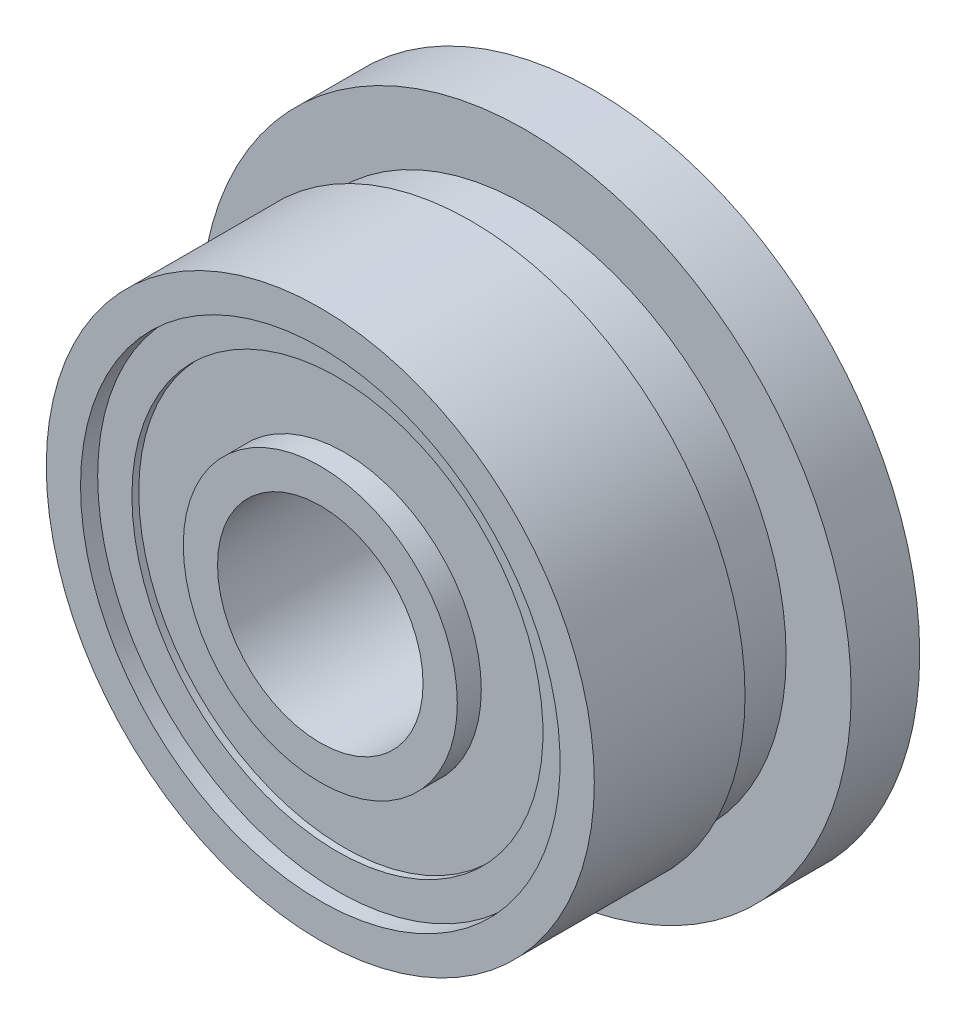
SolidWorks part; units mm, degrees
ref_plane "Piano frontale" through (0, 0, 0) normal (0, 0, 1) x (1, 0, 0)
ref_plane "Piano superiore" through (0, 0, 0) normal (0, 1, 0) x (1, 0, 0)
ref_plane "Piano destro" through (0, 0, 0) normal (1, 0, 0) x (0, 0, -1)
sketch "Schizzo1" plane through (0, 0, 0) normal (0, 0, 1) x (1, 0, 0)
  circle A0 centre (0, 0) radius 4
  dimension "D1" = 8
extrude "Estrusione-Estrusione1" add sketch "Schizzo1" along normal blind 4
sketch "Schizzo2" plane through (0, 0, 4) normal (0, 0, 1) x (1, 0, 0)
  circle A0 centre (0, 0) radius 1.5
  dimension "D1" = 3
extrude "Taglio-Estrusione1" cut sketch "Schizzo2" against normal through all
sketch "Schizzo3" plane through (0, 0, 0) normal (0, 0, -1) x (-1, 0, 0)
  circle A0 centre (0, 0) radius 3.5
  circle A1 centre (0, 0) radius 2
  dimension "D1" = 7
  dimension "D2" = 4
extrude "Taglio-Estrusione2" cut sketch "Schizzo3" against normal blind 0.25
sketch "Schizzo4" plane through (0, 0, 0.25) normal (0, 0, -1) x (-1, 0, 0)
  circle A0 centre (0, 0) radius 3
  circle A1 centre (0, 0) radius 2 construction
  circle A2 centre (0, 0) radius 2
  dimension "D1" = 6
extrude "Taglio-Estrusione3" cut sketch "Schizzo4" against normal blind 0.1
ref_plane "Piano1" through (0, 0, 2) normal (0, 0, 1) x (1, 0, 0)
mirror "Specchia1" about plane through (0, 0, 2) normal (0, 0, 1) of "Taglio-Estrusione3", "Taglio-Estrusione2"
sketch "Schizzo5" plane through (0, 0, 0) normal (0, 0, 1) x (1, 0, 0)
  circle A0 centre (0, 0) radius 4.75
  circle A1 centre (0, 0) radius 4 construction
  circle A2 centre (0, 0) radius 4
  dimension "D1" = 9.5
extrude "Estrusione-Estrusione2" add sketch "Schizzo5" along normal blind 1
sketch "Schizzo6" plane through (0, 0, 0) normal (0, 1, 0) x (1, 0, 0)
  line L1 (4, -1) -> (3.8, -1)
  line L2 (4, -1) -> (4, -1.8)
  line L3 (4, -1.8) -> (3.8, -1.8)
  line L4 (3.8, -1) -> (3.8, -1.8)
  dimension "D1" = 0.8
  dimension "D2" = 0.2
revolve "Taglia-Rivoluzione1" cut sketch "Schizzo6" angle 360 about axis through (0, 0, 4) along (0, 0, -1)
